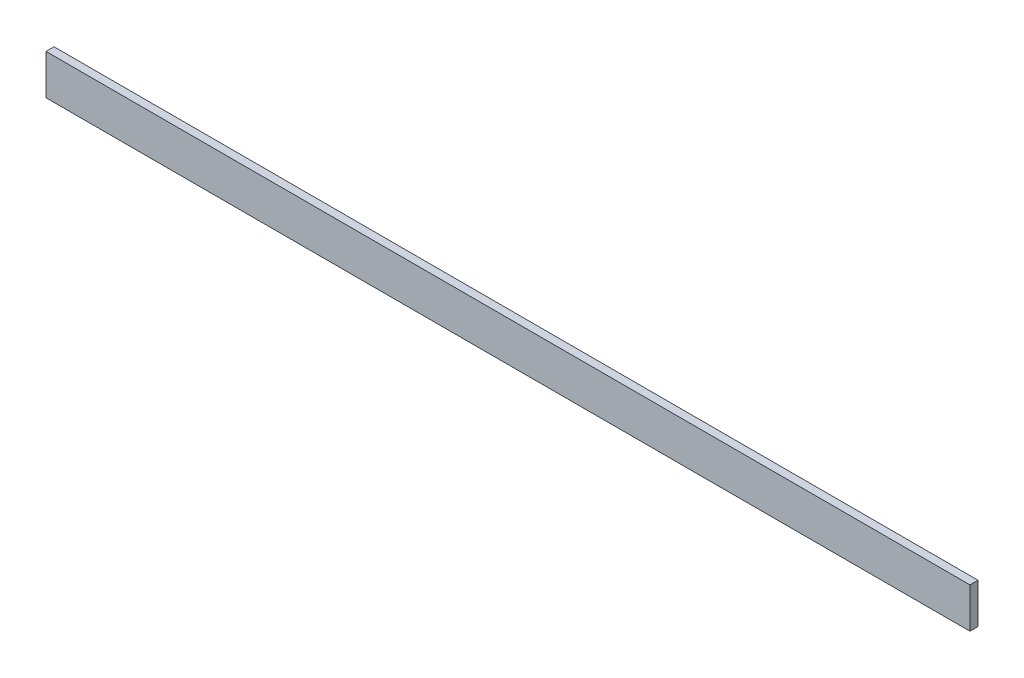
SolidWorks part; units mm, degrees
ref_plane "Plano frontal" through (0, 0, 0) normal (0, 0, 1) x (1, 0, 0)
ref_plane "Plano superior" through (0, 0, 0) normal (0, 1, 0) x (1, 0, 0)
ref_plane "Plano direito" through (0, 0, 0) normal (1, 0, 0) x (0, 0, -1)
sketch "Esboço1" plane through (0, 0, 0) normal (0, 0, 1) x (1, 0, 0)
  line L1 (0, 0) -> (2300, 0)
  line L2 (0, 0) -> (0, 100)
  line L3 (0, 100) -> (2300, 100)
  line L4 (2300, 0) -> (2300, 100)
  dimension "D1" = 2300
  dimension "D2" = 100
extrude "Ressalto-extrusão1" add sketch "Esboço1" along normal blind 20
